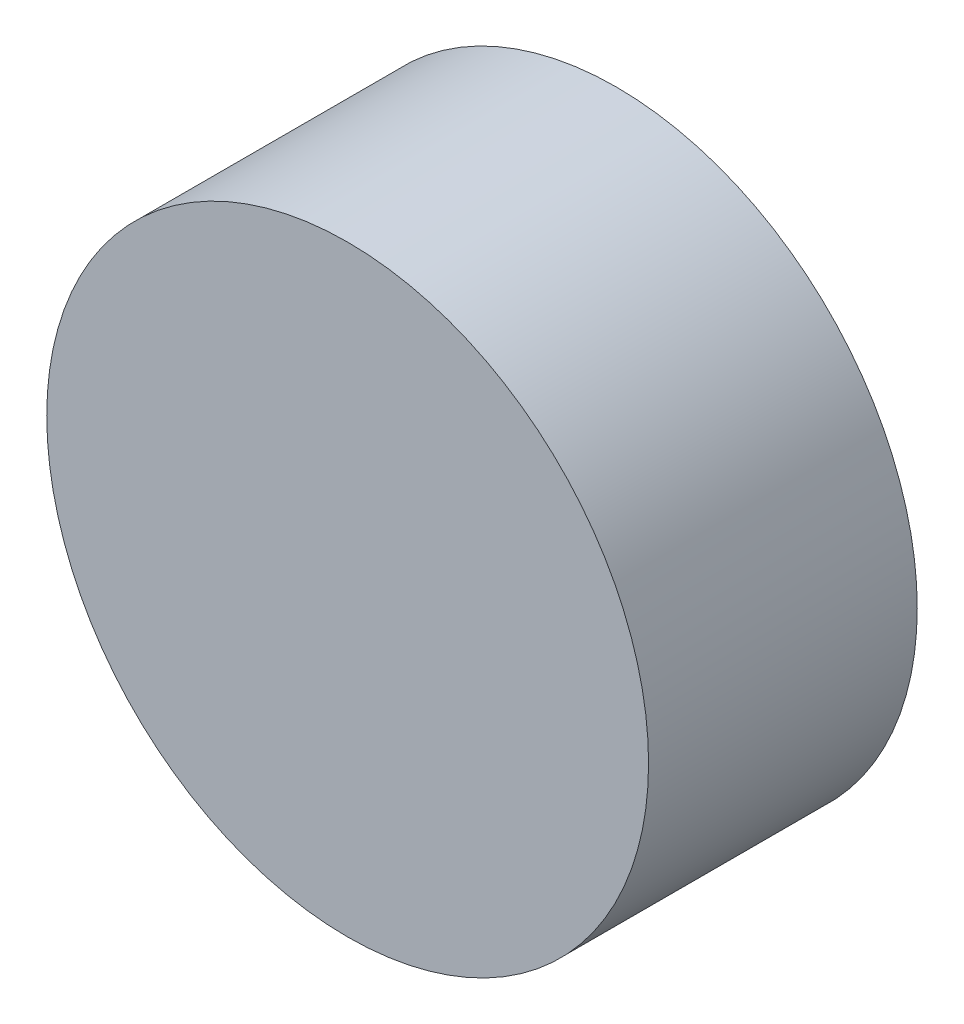
SolidWorks part; units mm, degrees
ref_plane "前基準面" through (0, 0, 0) normal (0, 0, 1) x (1, 0, 0)
ref_plane "上基準面" through (0, 0, 0) normal (0, 1, 0) x (1, 0, 0)
ref_plane "右基準面" through (0, 0, 0) normal (1, 0, 0) x (0, 0, -1)
sketch "草圖1" plane through (0, 0, 0) normal (0, 0, 1) x (1, 0, 0)
  circle A0 centre (0, 0) radius 5.6
  dimension "D1" = 11.2
extrude "填料-伸長1" add sketch "草圖1" along normal blind 5
